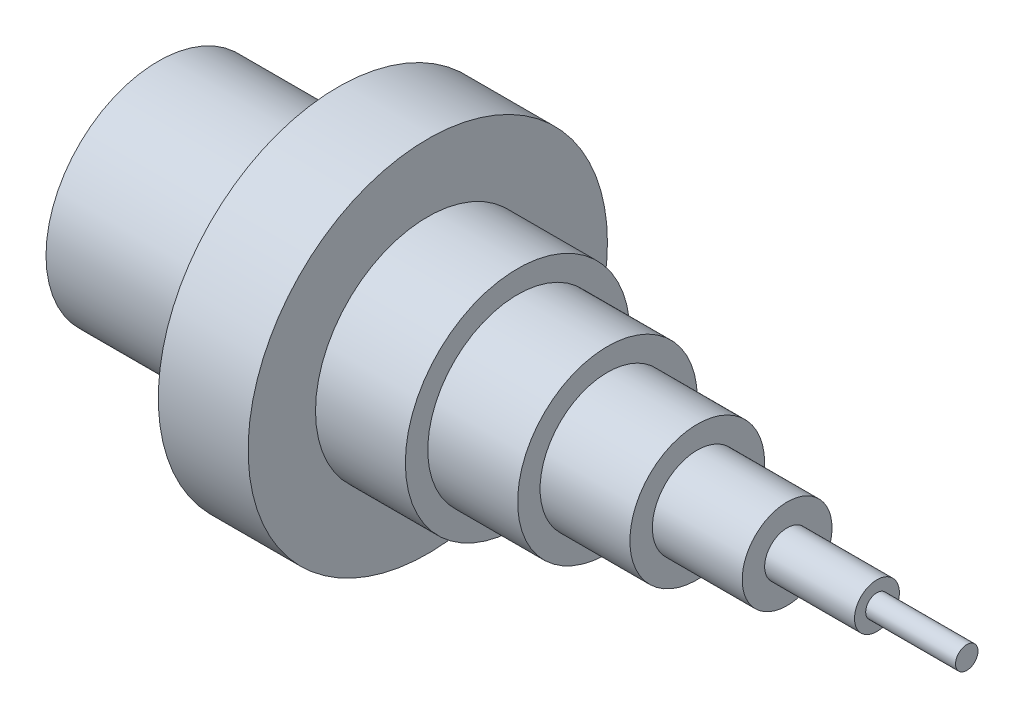
SolidWorks part; units mm, degrees
ref_plane "Front Plane" through (0, 0, 0) normal (0, 0, 1) x (1, 0, 0)
ref_plane "Top Plane" through (0, 0, 0) normal (0, 1, 0) x (1, 0, 0)
ref_plane "Right Plane" through (0, 0, 0) normal (1, 0, 0) x (0, 0, -1)
sketch "Sketch1" plane through (0, 0, 0) normal (1, 0, 0) x (0, 0, -1)
  circle A0 centre (0, 0) radius 25
  dimension "D1" = 50
extrude "Boss-Extrude1" add sketch "Sketch1" along normal blind 40
sketch "Sketch2" plane through (0, 0, 0) normal (1, 0, 0) x (0, 0, -1)
  circle A0 centre (0, 0) radius 20
  dimension "D1" = 40
extrude "Cut-Extrude1" cut sketch "Sketch2" along normal blind 70
ref_plane "Plane1" through (40, 0, 0) normal (1, 0, 0) x (0, 0, -1)
ref_plane "Plane2" through (60, 0, 0) normal (1, 0, 0) x (0, 0, -1)
ref_plane "Plane3" through (80, 0, 0) normal (1, 0, 0) x (0, 0, -1)
ref_plane "Plane4" through (100, 0, 0) normal (1, 0, 0) x (0, 0, -1)
ref_plane "Plane5" through (120, 0, 0) normal (1, 0, 0) x (0, 0, -1)
ref_plane "Plane6" through (140, 0, 0) normal (1, 0, 0) x (0, 0, -1)
ref_plane "Plane7" through (160, 0, 0) normal (1, 0, 0) x (0, 0, -1)
sketch "Sketch3" plane through (40, 0, 0) normal (1, 0, 0) x (0, 0, -1)
  circle A0 centre (0, 0) radius 40
  dimension "D1" = 80
sketch "Sketch4" plane through (60, 0, 0) normal (1, 0, 0) x (0, 0, -1)
  circle A0 centre (0, 0) radius 25
sketch "Sketch5" plane through (80, 0, 0) normal (1, 0, 0) x (0, 0, -1)
  circle A0 centre (0, 0) radius 20
sketch "Sketch6" plane through (100, 0, 0) normal (1, 0, 0) x (0, 0, -1)
  circle A0 centre (0, 0) radius 15
  dimension "D1" = 30
sketch "Sketch7" plane through (120, 0, 0) normal (1, 0, 0) x (0, 0, -1)
  circle A0 centre (0, 0) radius 10
  dimension "D1" = 20
sketch "Sketch8" plane through (140, 0, 0) normal (1, 0, 0) x (0, 0, -1)
  circle A0 centre (0, 0) radius 5
  dimension "D1" = 10
sketch "Sketch9" plane through (160, 0, 0) normal (1, 0, 0) x (0, 0, -1)
  circle A0 centre (0, 0) radius 2.5
  dimension "D1" = 5
extrude "Boss-Extrude2" add sketch "Sketch9" along normal blind 20 separate body
extrude "Boss-Extrude3" add sketch "Sketch3" along normal blind 20 contours A0
extrude "Boss-Extrude4" add sketch "Sketch4" along normal blind 20 contours A0
extrude "Boss-Extrude5" add sketch "Sketch5" along normal blind 20 contours A0
extrude "Boss-Extrude6" add sketch "Sketch6" along normal blind 20 contours A0
extrude "Boss-Extrude7" add sketch "Sketch7" along normal blind 20 contours A0
extrude "Boss-Extrude8" add sketch "Sketch8" along normal blind 20 contours A0
